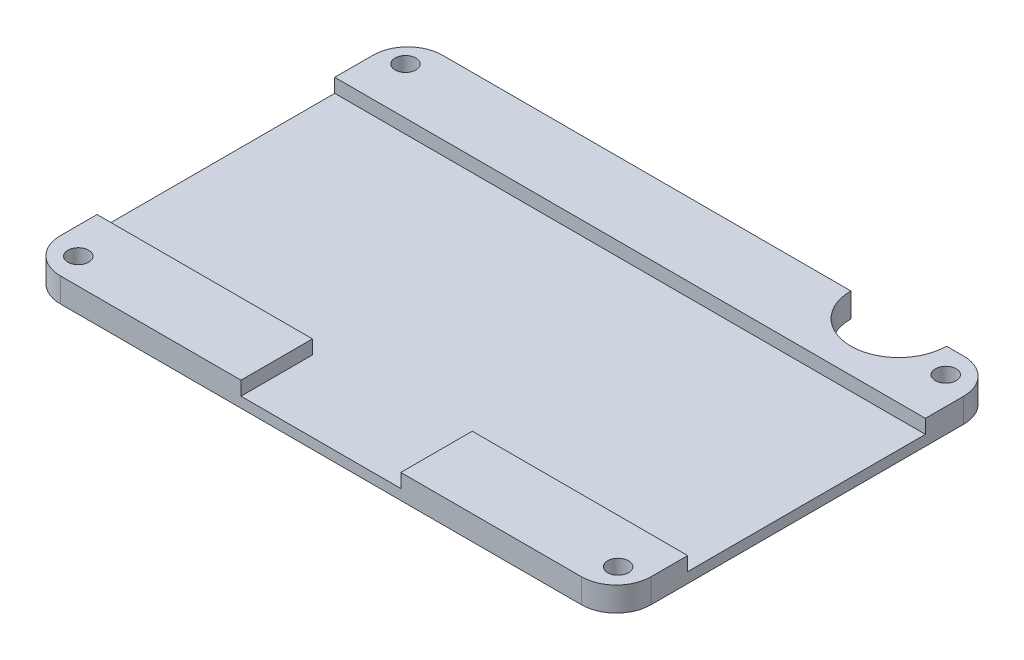
SolidWorks part; units mm, degrees
ref_plane "Front Plane" through (0, 0, 0) normal (0, 0, 1) x (1, 0, 0)
ref_plane "Top Plane" through (0, 0, 0) normal (0, 1, 0) x (1, 0, 0)
ref_plane "Right Plane" through (0, 0, 0) normal (1, 0, 0) x (0, 0, -1)
sketch "Sketch1" plane through (0, 0, 0) normal (0, 1, 0) x (1, 0, 0)
  line L1 (-20.6225, 7.5653) -> (54.3775, 7.5653)
  line L2 (-25.6225, 2.5653) -> (-25.6225, -42.4347)
  line L3 (-20.6225, -47.4347) -> (54.3775, -47.4347)
  line L4 (59.3775, 2.5653) -> (59.3775, -42.4347)
  arc A0 (54.3775, -47.4347) -> (59.3775, -42.4347) centre (54.3775, -42.4347) ccw
  arc A1 (-20.6225, -47.4347) -> (-25.6225, -42.4347) centre (-20.6225, -42.4347) cw
  arc A2 (59.3775, 2.5653) -> (54.3775, 7.5653) centre (54.3775, 2.5653) ccw
  arc A3 (-25.6225, 2.5653) -> (-20.6225, 7.5653) centre (-20.6225, 2.5653) cw
  point P7 (59.3775, -47.4347)
  point P12 (59.3775, 7.5653)
  point P15 (-25.6225, 7.5653)
  dimension "D3" = 5
  dimension "D1" = 85
  dimension "D2" = 55
extrude "Boss-Extrude1" add sketch "Sketch1" along normal blind 3.5
sketch "Sketch2" plane through (0, 3.5, 0) normal (0, 1, 0) x (1, 0, 0)
  circle A0 centre (-22.1876, 3.8027) radius 2.8
  circle A3 centre (-21.7754, -43.6973) radius 2.8
  circle A4 centre (55.4124, 3.9479) radius 2.8
  circle A5 centre (55.7665, -43.5521) radius 2.8
  circle A6 centre (-22.1876, 3.8027) radius 1.5
  circle A7 centre (55.4124, 3.9479) radius 1.5
  circle A8 centre (55.7665, -43.5521) radius 1.5
  circle A9 centre (-21.7754, -43.6973) radius 1.5
  dimension "D1" = 47.5
  dimension "D2" = 47.5
  dimension "D3" = 77.6
extrude "Cut-Extrude1" cut sketch "Sketch2" against normal blind 3.5 contours A9 | A8 | A7 | A6
sketch "Sketch3" plane through (0, 3.5, 0) normal (0, 1, 0) x (1, 0, 0)
  line L0 (-25.6225, 2.5653) -> (-25.6225, -42.4347) construction
  line L1 (-25.6225, -2.9473) -> (59.3775, -2.9473)
  line L2 (-25.6225, -2.9473) -> (-25.6225, -37.151)
  line L3 (-25.6225, -37.151) -> (59.3775, -37.151)
  line L4 (59.3775, -2.9473) -> (59.3775, -37.151)
  line L5 (59.3775, -42.4347) -> (59.3775, 2.5653) construction
  line L6 (5.3775, -37.151) -> (5.3775, -47.4347)
  line L7 (-20.6225, -47.4347) -> (54.3775, -47.4347) construction
  line L8 (5.3775, -47.4347) -> (28.3775, -47.4347)
  line L9 (28.3775, -47.4347) -> (28.3775, -37.151)
  circle A0 centre (-22.1876, 3.8027) radius 1.5 construction
  line M12 (59.3775, -42.4347) -> (59.3775, 2.5653)
  line M16 (-25.6225, 2.5653) -> (-25.6225, -42.4347)
  line M18 (-20.6225, -47.4347) -> (54.3775, -47.4347)
  dimension "D2" = 23
  dimension "D1" = 6.75
  dimension "D3" = 31
extrude "Cut-Extrude2" cut sketch "Sketch3" against normal blind 2 contours L9 L3 L6 M18 | L3 L1 M16 M12
sketch "Sketch9" plane through (0, 3.5, 0) normal (0, 1, 0) x (1, 0, 0)
  line L0 (54.3775, 7.5653) -> (-20.6225, 7.5653) construction
  line L1 (38.1394, 7.5653) -> (51.7198, 7.5653)
  line L6 (-25.6225, 2.5653) -> (-25.6225, -2.9473)
  line L7 (-25.6225, -2.9473) -> (59.3775, -2.9473)
  line L8 (59.3775, -2.9473) -> (59.3775, 2.5653)
  line L9 (54.3775, 7.5653) -> (-20.6225, 7.5653)
  line L13 (51.9006, 7.5653) -> (51.7198, 7.5653)
  arc A0 (51.9006, 7.5653) -> (38.1394, 7.5653) centre (45.02, 7.5653) cw
  arc A3 (59.3775, 2.5653) -> (54.3775, 7.5653) centre (54.3775, 2.5653) ccw
  arc A4 (-20.6225, 7.5653) -> (-25.6225, 2.5653) centre (-20.6225, 2.5653) ccw
  dimension "D1" = 0
extrude "Cut-Extrude6" cut sketch "Sketch9" against normal blind 3.5 contours L13 L1 A0
